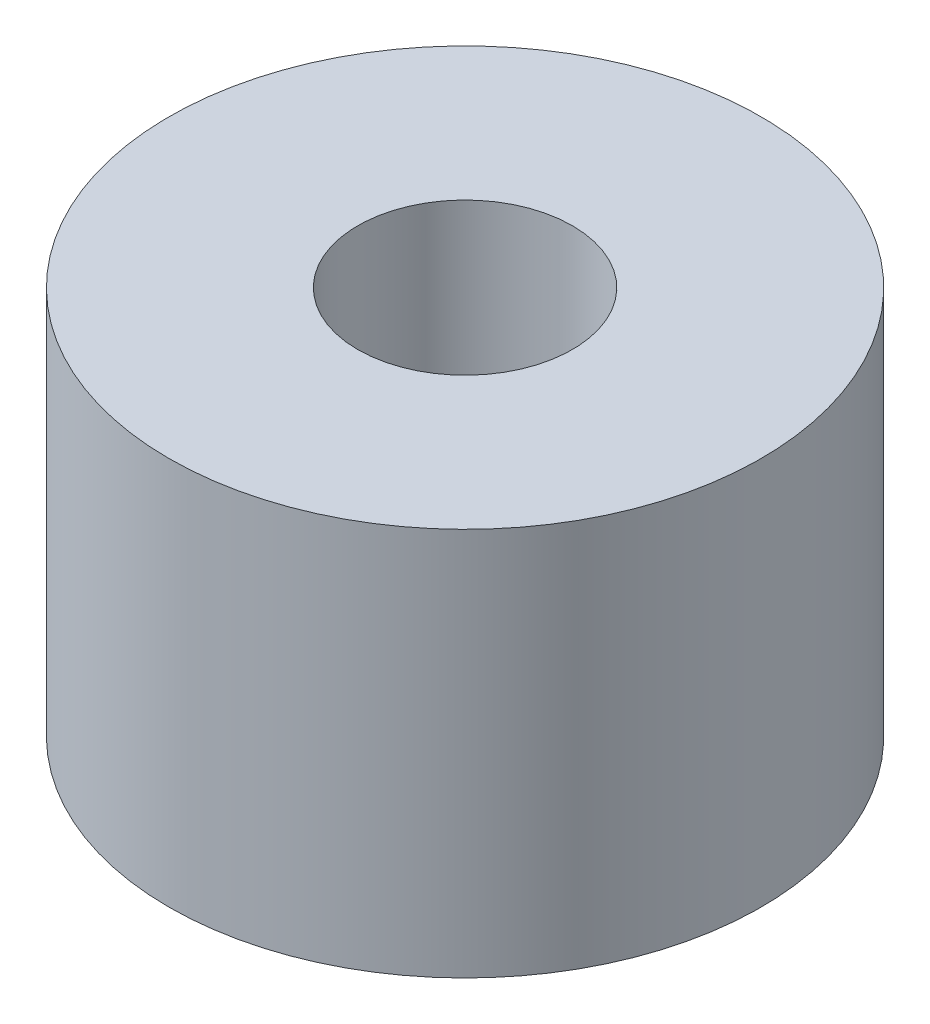
SolidWorks part; units mm, degrees
ref_plane "Plan de face" through (0, 0, 0) normal (0, 0, 1) x (1, 0, 0)
ref_plane "Plan de dessus" through (0, 0, 0) normal (0, 1, 0) x (1, 0, 0)
ref_plane "Plan de droite" through (0, 0, 0) normal (1, 0, 0) x (0, 0, -1)
sketch "Esquisse1" plane through (0, 0, 0) normal (0, 1, 0) x (1, 0, 0)
  circle A0 centre (0, 0) radius 4
  circle A1 centre (0, 0) radius 1.45
  dimension "D1" = 8
  dimension "D2" = 2.9
extrude "Boss.-Extru.1" add sketch "Esquisse1" along normal blind 5.25
